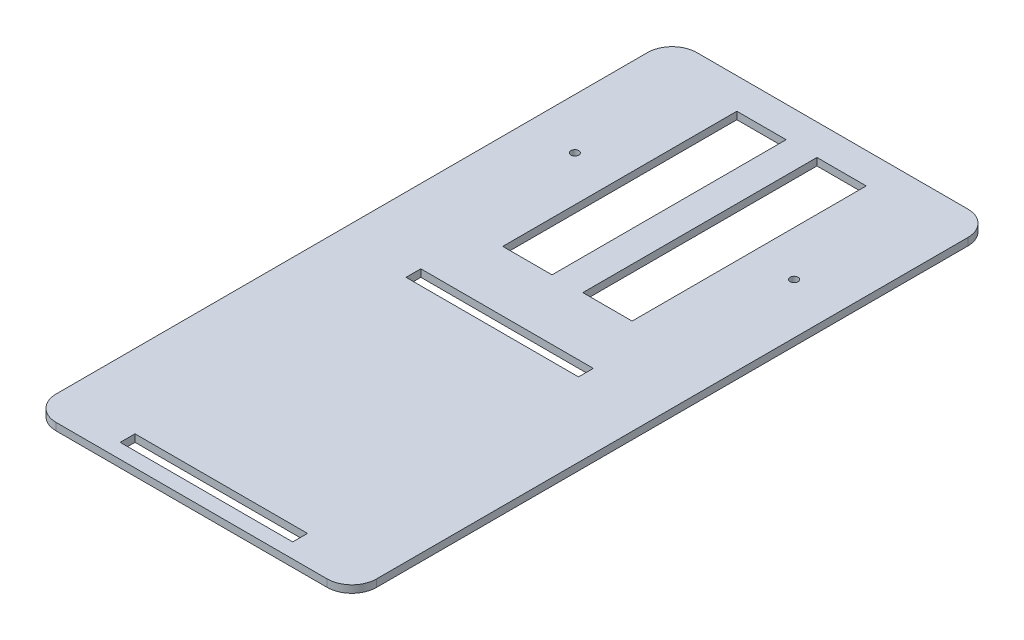
SolidWorks part; units mm, degrees
ref_plane "Front Plane" through (0, 0, 0) normal (0, 0, 1) x (1, 0, 0)
ref_plane "Top Plane" through (0, 0, 0) normal (0, 1, 0) x (1, 0, 0)
ref_plane "Right Plane" through (0, 0, 0) normal (1, 0, 0) x (0, 0, -1)
sketch "Sketch1" plane through (0, 0, 0) normal (0, 1, 0) x (1, 0, 0)
  line L1 (-65, -60) -> (65, -60)
  line L2 (-65, -60) -> (-65, 60)
  line L3 (-65, 60) -> (65, 60)
  line L4 (65, -60) -> (65, 60)
  line L5 (-65, -60) -> (65, 60) construction
  line L6 (-65, 60) -> (65, -60) construction
  point P0 (0, 0)
  dimension "D1" = 130
  dimension "D2" = 120
extrude "Boss-Extrude1" add sketch "Sketch1" along normal blind 3
sketch "Sketch2" plane through (0, 3, 0) normal (0, 1, 0) x (1, 0, 0)
  line L1 (-26.25, -47.5) -> (-6.25, -47.5)
  line L2 (-26.25, -47.5) -> (-26.25, 47.5)
  line L3 (-26.25, 47.5) -> (-6.25, 47.5)
  line L4 (-6.25, -47.5) -> (-6.25, 47.5)
  line L5 (-26.25, -47.5) -> (-6.25, 47.5) construction
  line L6 (-26.25, 47.5) -> (-6.25, -47.5) construction
  point P0 (-16.25, 0)
  dimension "D1" = 95
  dimension "D2" = 20
  dimension "D3" = 6.25
extrude "Cut-Extrude1" cut sketch "Sketch2" against normal through all both and the other way through all
mirror "Mirror1" about plane through (0, 0, 0) normal (1, 0, 0) of "Cut-Extrude1"
sketch "Sketch3" plane through (0, 3, 0) normal (0, 1, 0) x (1, 0, 0)
  circle A0 centre (44.5, 0) radius 1.6
  dimension "D1" = 3.2
  dimension "D2" = 44.5
extrude "Cut-Extrude2" cut sketch "Sketch3" against normal through all both and the other way through all
mirror "Mirror2" about plane through (0, 0, 0) normal (1, 0, 0) of "Cut-Extrude2"
sketch "Sketch4" plane through (0, 0, 60) normal (0, 0, 1) x (1, 0, 0)
  line L4 (-65, 0) -> (65, 0)
  line L5 (65, 0) -> (65, 3)
  line L6 (65, 3) -> (-65, 3)
  line L7 (-65, 3) -> (-65, 0)
  line L8 (-65, 0) -> (65, 0)
  line L9 (65, 0) -> (65, 3)
  line L10 (65, 3) -> (-65, 3)
  line L11 (-65, 3) -> (-65, 0)
  dimension "D1" = 0
extrude "Boss-Extrude2" add sketch "Sketch4" along normal blind 140
sketch "Sketch5" plane through (0, 3, 0) normal (0, 1, 0) x (1, 0, 0)
  line L1 (-35, -78) -> (35, -78)
  line L2 (-35, -78) -> (-35, -72)
  line L3 (-35, -72) -> (35, -72)
  line L4 (35, -78) -> (35, -72)
  line L5 (-35, -78) -> (35, -72) construction
  line L6 (-35, -72) -> (35, -78) construction
  line L7 (-35, -194) -> (35, -194)
  line L8 (-35, -194) -> (-35, -188)
  line L9 (-35, -188) -> (35, -188)
  line L10 (35, -194) -> (35, -188)
  line L11 (-35, -194) -> (35, -188) construction
  line L12 (-35, -188) -> (35, -194) construction
  point P0 (0, -75)
  point P5 (0, -191)
  point P10 (0, 0)
  dimension "D1" = 6
  dimension "D2" = 6
  dimension "D3" = 70
  dimension "D4" = 70
  dimension "D5" = 75
  dimension "D6" = 110
extrude "Cut-Extrude3" cut sketch "Sketch5" against normal through all both and the other way through all
fillet "Fillet1" radius 10 4 edges at (65, 1.5, 200) (-65, 1.5, 200) (65, 1.5, -60) (-65, 1.5, -60)
